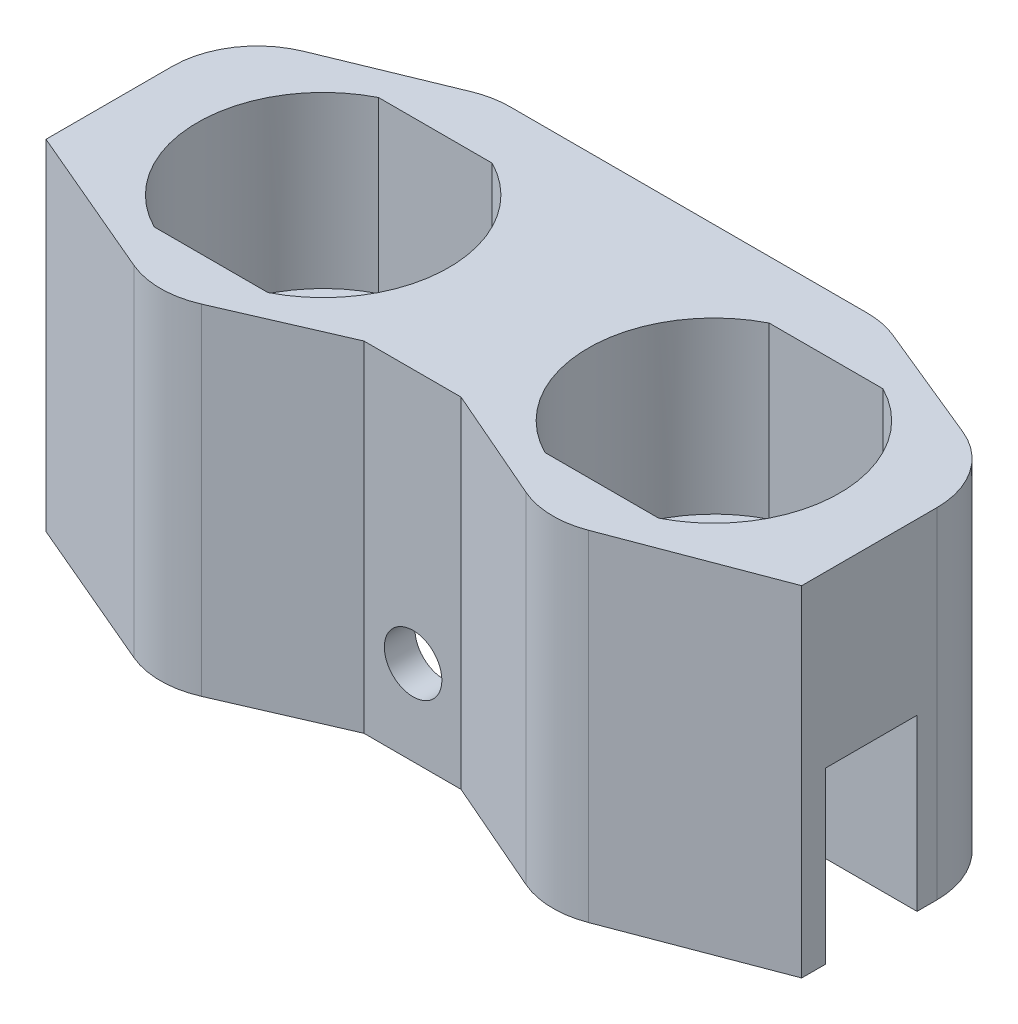
SolidWorks part; units mm, degrees
ref_plane "Front Plane" through (0, 0, 0) normal (0, 0, 1) x (1, 0, 0)
ref_plane "Top Plane" through (0, 0, 0) normal (0, 1, 0) x (1, 0, 0)
ref_plane "Right Plane" through (0, 0, 0) normal (1, 0, 0) x (0, 0, -1)
sketch "Sketch1" plane through (0, 0, 0) normal (0, 1, 0) x (1, 0, 0)
  line L0 (-4.2502, 8.382) -> (4.2502, 8.382)
  line L1 (-4.2502, -8.382) -> (4.2502, -8.382)
  line L2 (24.9598, 8.382) -> (33.4602, 8.382)
  line L3 (-13.97, 12.7) -> (43.18, 12.7)
  line L4 (-13.97, 12.7) -> (-13.97, -12.7)
  line L5 (-13.97, -12.7) -> (43.18, -12.7)
  line L6 (43.18, 12.7) -> (43.18, -12.7)
  line L7 (24.9598, -8.382) -> (33.4602, -8.382)
  line L8 (14.605, 12.7) -> (14.605, -12.7) construction
  line L9 (0, 0) -> (29.21, 0) construction
  arc A0 (4.2502, -8.382) -> (4.2502, 8.382) centre (0, 0) ccw
  arc A2 (-4.2502, 8.382) -> (-4.2502, -8.382) centre (0, 0) ccw
  arc A3 (24.9598, 8.382) -> (24.9598, -8.382) centre (29.21, 0) ccw
  arc A4 (33.4602, -8.382) -> (33.4602, 8.382) centre (29.21, 0) ccw
  point P17 (14.605, 0)
  point P18 (14.605, 0)
  dimension "D1" = 9.398
  dimension "D3" = 2
  dimension "D2" = 16.764
  dimension "D4" = 57.15
  dimension "D5" = 25.4
extrude "Boss-Extrude1" add sketch "Sketch1" along normal blind 12.7
sketch "Sketch3" plane through (0, 0, 0) normal (0, -1, 0) x (1, 0, 0)
  line L0 (-13.97, -12.7) -> (-13.97, 12.7) construction
  line L1 (-13.97, 12.7) -> (43.18, 12.7)
  line L2 (-13.97, 12.7) -> (-13.97, 5.6418)
  line L3 (-13.97, 5.6418) -> (-2.7278, 5.6418)
  line L4 (43.18, 12.7) -> (43.18, 5.6418)
  line L5 (-13.97, 12.7) -> (43.18, 12.7) construction
  line L6 (43.18, 12.7) -> (43.18, -12.7) construction
  line L7 (-4.2502, 8.382) -> (4.2502, 8.382) construction
  line L14 (43.18, -1.2162) -> (43.18, -12.7)
  line L15 (43.18, -12.7) -> (-13.97, -12.7)
  line L16 (43.18, -12.7) -> (-13.97, -12.7) construction
  line L17 (-13.97, -12.7) -> (-13.97, -1.2162)
  line L38 (32.0935, 5.6418) -> (43.18, 5.6418)
  line L39 (43.18, -1.2162) -> (34.7022, -1.2162)
  line L40 (24.9598, 8.382) -> (33.4602, 8.382) construction
  line L41 (2.7278, 5.6418) -> (26.3265, 5.6418)
  line L42 (-5.5841, -1.2162) -> (-13.97, -1.2162)
  line L43 (23.7178, -1.2162) -> (5.5841, -1.2162)
  line L44 (-2.7278, 5.6418) -> (2.7278, 5.6418)
  line L45 (26.3265, 5.6418) -> (32.0935, 5.6418)
  arc A4 (-5.5841, -1.2162) -> (5.5841, -1.2162) centre (0, 0) ccw
  arc A5 (23.7178, -1.2162) -> (34.7022, -1.2162) centre (29.21, 0) ccw
  point P23 (29.21, 8.382)
  dimension "D3" = 11.43
  dimension "D1" = 2.7402
  dimension "D2" = 6.858
extrude "Boss-Extrude3" add sketch "Sketch3" along normal blind 12.7
ref_plane "Plane1" through (14.605, 0, 0) normal (1, 0, 0) x (0, 0, -1)
sketch "Sketch4" plane through (0, -12.7, 0) normal (0, -1, 0) x (1, 0, 0)
  line L0 (-13.97, -12.7) -> (43.18, -12.7) construction
  line L1 (-13.97, -1.2162) -> (-13.97, -12.7) construction
  line L2 (43.18, -12.7) -> (43.18, -1.2162) construction
  line L3 (0, -5.715) -> (0, -12.7) construction
  line L4 (29.21, -12.7) -> (29.21, -5.6252) construction
  line L5 (-13.97, -6.9581) -> (-13.97, -12.7)
  line L6 (-13.97, -12.7) -> (0, -12.7)
  line L7 (29.21, -12.7) -> (43.18, -12.7)
  line L8 (43.18, -12.7) -> (43.18, -6.9581)
  line L9 (0, -12.7) -> (-13.97, -6.9581)
  line L10 (29.21, -12.7) -> (43.18, -6.9581)
  line L11 (43.18, 9.1709) -> (43.18, 5.6418) construction
  line L12 (43.18, 5.6418) -> (43.18, 12.7) construction
  line L16 (43.18, 12.7) -> (43.18, 7.4063)
  line L17 (29.21, -5.6252) -> (29.21, 12.7) construction
  line L18 (0, -5.715) -> (0, 12.7) construction
  line L19 (43.18, 12.7) -> (-13.97, 12.7) construction
  line L23 (43.18, 7.4063) -> (29.21, 12.7)
  line L31 (29.21, 12.7) -> (43.18, 12.7)
  line L32 (0, 12.7) -> (-13.97, 6.751)
  line L33 (-13.97, 12.7) -> (-13.97, 5.6418) construction
  line L34 (-13.97, 6.751) -> (-13.97, 12.7)
  line L35 (-13.97, 12.7) -> (0, 12.7)
  arc A2 (-5.5841, -1.2162) -> (5.5841, -1.2162) centre (0, 0) ccw construction
  arc A3 (23.7178, -1.2162) -> (34.7022, -1.2162) centre (29.21, 0) ccw construction
extrude "Cut-Extrude1" cut sketch "Sketch4" against normal through all
sketch "Sketch5" plane through (0, -12.7, 0) normal (0, -1, 0) x (1, 0, 0)
  line L0 (0, 12.7) -> (14.605, 6.35)
  line L1 (29.21, 12.7) -> (0, 12.7) construction
  line L2 (14.605, 6.35) -> (29.21, 12.7)
  line L3 (29.21, 12.7) -> (0, 12.7)
  dimension "D1" = 6.35
extrude "Cut-Extrude2" cut sketch "Sketch5" against normal through all
fillet "Fillet1" radius 6.35 6 edges at (-13.97, 0, -6.9581) (0, 0, -12.7) (29.21, 0, -12.7) (43.18, 0, -6.9581) (29.21, 0, 12.7) (0, 0, 12.7)
sketch "Sketch7" plane through (0, -12.7, 0) normal (0, -1, 0) x (1, 0, 0)
  line L0 (-13.97, 5.6418) -> (43.18, 5.6418) construction
  line L1 (8.255, 5.6418) -> (20.955, 5.6418)
  line L2 (8.255, 5.6418) -> (8.255, 7.9278)
  line L3 (8.255, 7.9278) -> (20.955, 7.9278)
  line L4 (20.955, 5.6418) -> (20.955, 7.9278)
  point P6 (14.605, 5.6418)
  point P7 (14.605, 7.9278)
  dimension "D1" = 12.7
  dimension "D2" = 2.286
extrude "Boss-Extrude4" add sketch "Sketch7" against normal up to surface (25.4 mm away) up to face at (14.6069, 12.7, -0.3766)
sketch "Sketch6" plane through (0, 0, -1.2162) normal (0, 0, 1) x (1, 0, 0)
  line L0 (23.7178, -12.7) -> (5.5841, -12.7) construction
  circle A0 centre (14.6509, -6.35) radius 2.15
  point P4 (14.6509, -12.7)
  dimension "D1" = 4.3
  dimension "D2" = 6.35
extrude "Cut-Extrude3" cut sketch "Sketch6" against normal through all both and the other way through all
